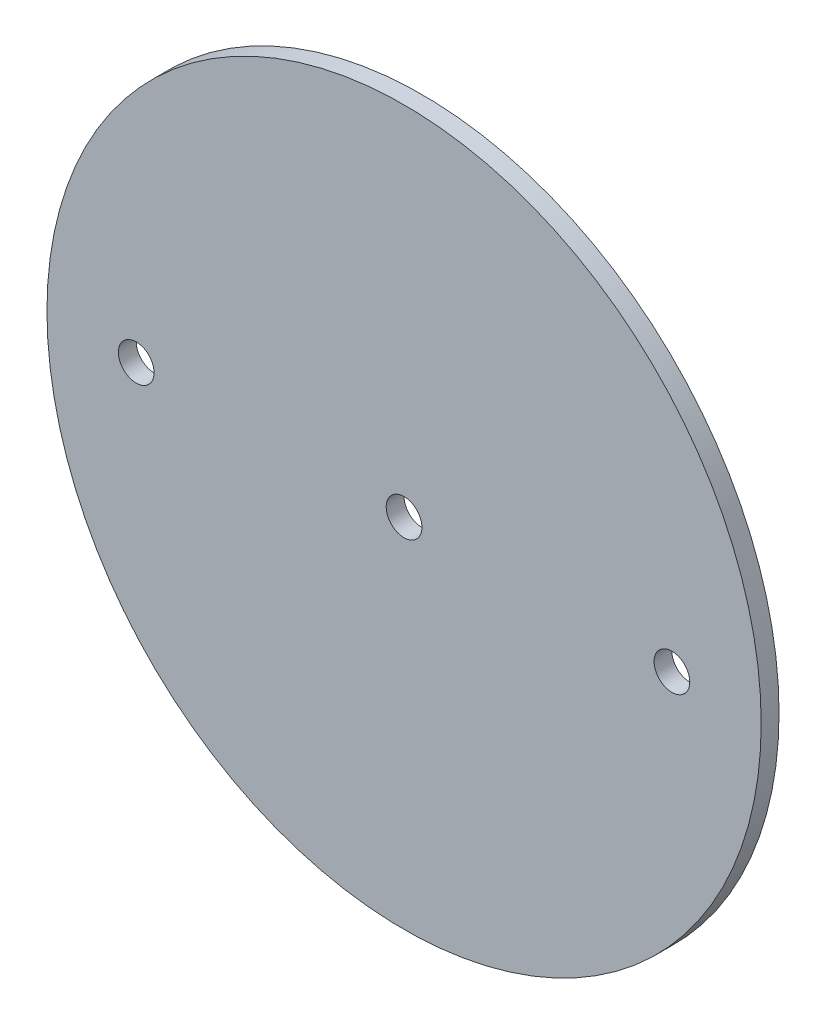
SolidWorks part; units mm, degrees
ref_plane "Front Plane" through (0, 0, 0) normal (0, 0, 1) x (1, 0, 0)
ref_plane "Top Plane" through (0, 0, 0) normal (0, 1, 0) x (1, 0, 0)
ref_plane "Right Plane" through (0, 0, 0) normal (1, 0, 0) x (0, 0, -1)
sketch "Sketch1" plane through (0, 0, 0) normal (0, 0, 1) x (1, 0, 0)
  circle A0 centre (0, 0) radius 63.5
  dimension "D1" = 127
extrude "Boss-Extrude1" add sketch "Sketch1" along normal mid plane 3.175
sketch "Sketch2" plane through (0, 0, 1.5875) normal (0, 0, 1) x (1, 0, 0)
  line L0 (-1000, 0) -> (49000, 0) construction
  point P1 (0, 0)
  point P4 (47.625, 0)
  point P5 (-47.625, 0)
  dimension "D1" = 47.625
  dimension "D2" = 95.25
hole_wizard "1/4 (0.25) Diameter Hole1" positions "Sketch2" profile "Sketch3" hole size "1/4" standard "ANSI Inch" end condition through all
sketch "Sketch3" plane through (-47.625, 0, 1.5875) normal (1, 0, 0) x (0, -1, 0)
  line L0 (0, 0) -> (0, 3.175)
  line L1 (0, 3.175) -> (3.175, 3.175)
  line L2 (3.175, 3.175) -> (3.175, 0)
  line L5 (3.175, 0) -> (0, 0)
  line L11 (0, -6.35) -> (0, 107.95) construction
  dimension "Thru Hole Dia." = 6.35
  dimension "Thru Hole Depth" = 3.175
equation "\"AIRFRAME_OD\"= 5.15in"
equation "\"AIRFRAME_ID\"= 5.00in"
equation "\"FLAT_T\"= 0.125in"
equation "\"NOSE_EXP_L\"= 27in"
equation "\"NOSE_SHOULDER_L\"= 5in"
equation "\"MAIN_L\"= 30in"
equation "\"RECO_COUP_L\"= 10in"
equation "\"RECO_SWITCH_L\"= 2in"
equation "\"DROGUE_L\"= 20in"
equation "\"ATS_FORE_COUP_L\"= 5.5in"
equation "\"ATS_AFT_COUP_L\"= 4.5in"
equation "\"LOWER_L\"= 30in"
equation "\"FIN_N\"= 4"
equation "\"CR_AFT_X\"= 0.5in"
equation "\"CR_FORE_X\"= 9.25in"
equation "\"FIN_ROOT\"= 8in"
equation "\"FIN_X\"= 0.75in"
equation "\"MOTOR_OD\"= 3.091in"
equation "\"MOTOR_ID\"= 3.00in"
equation "\"COUPLER_OD\"= 4.998in"
equation "\"COUPLER_ID\"= 4.88in"
equation "\"D1@Sketch1\"=\"AIRFRAME_ID\""
equation "\"D1@Boss-Extrude1\"=\"FLAT_T\""
equation "\"RECO_ROD_X\"= 3.5in"
equation "\"ATS_ROD_X\"= 3.75in"
equation "\"D1@Sketch2\"=\"ATS_ROD_X\"*0.5"
equation "\"D2@Sketch2\"=\"ATS_ROD_X\""
equation "\"MOTOR_L\"= 14in"
equation "\"MOTOR_LOWER_X\"= 2in"
